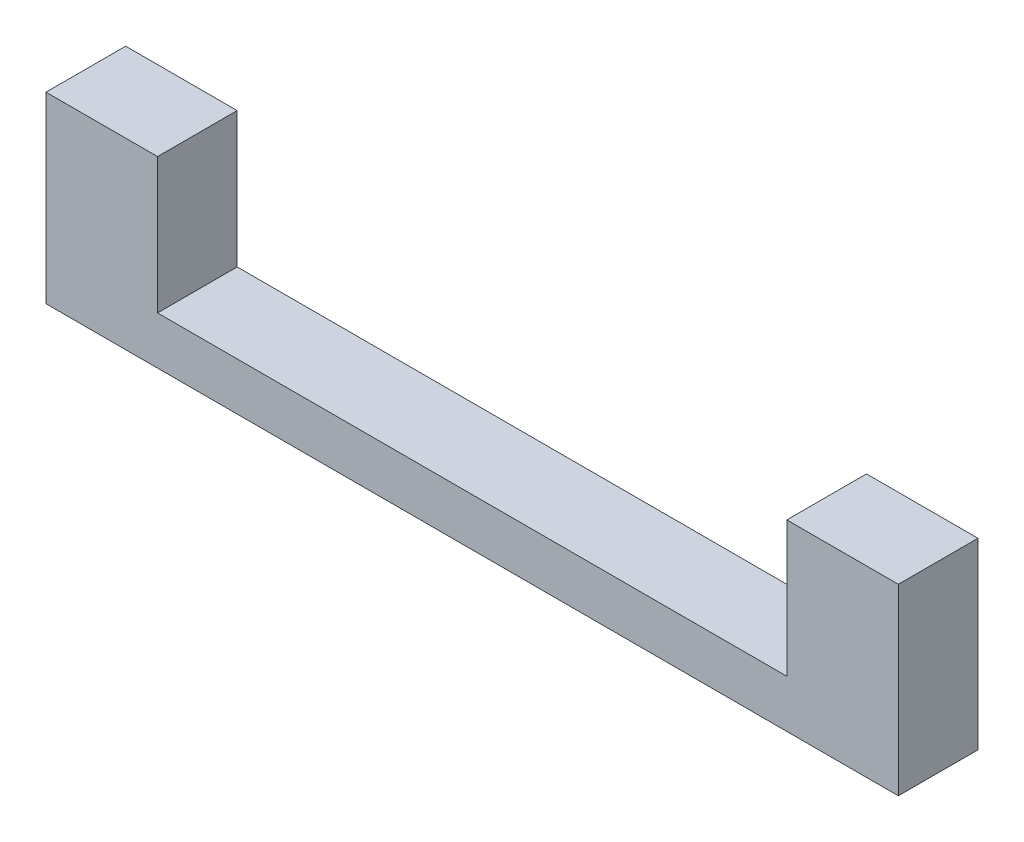
SolidWorks part; units mm, degrees
ref_plane "Front Plane" through (0, 0, 0) normal (0, 0, 1) x (1, 0, 0)
ref_plane "Top Plane" through (0, 0, 0) normal (0, 1, 0) x (1, 0, 0)
ref_plane "Right Plane" through (0, 0, 0) normal (1, 0, 0) x (0, 0, -1)
sketch "Sketch1" plane through (0, 0, 0) normal (1, 0, 0) x (0, 0, -1)
  line L0 (0, 0) -> (1.6017, 0) construction
  line L1 (1.705, 2.9531) -> (-1.705, 2.9531)
  line L2 (-1.705, 2.9531) -> (-3.41, 0)
  line L3 (-3.41, 0) -> (-1.705, -2.9531)
  line L4 (-1.705, -2.9531) -> (1.705, -2.9531)
  line L5 (1.705, -2.9531) -> (3.41, 0)
  line L6 (3.41, 0) -> (1.705, 2.9531)
  line L8 (-4.25, -4.25) -> (4.25, -4.25)
  line L9 (-4.25, -4.25) -> (-4.25, 4.25)
  line L10 (-4.25, 4.25) -> (4.25, 4.25)
  line L11 (4.25, -4.25) -> (4.25, 4.25)
  line L12 (-4.25, -4.25) -> (4.25, 4.25) construction
  line L13 (-4.25, 4.25) -> (4.25, -4.25) construction
  circle A0 centre (0, 0) radius 2.9531 construction
  dimension "D1" = 3.41
  dimension "D2" = 8.5
  dimension "D3" = 8.5
extrude "Boss-Extrude1" add sketch "Sketch1" along normal blind 5
sketch "Sketch2" plane through (0, 0, 0) normal (-1, 0, 0) x (0, 0, 1)
  line L1 (-4.25, -4.25) -> (4.25, -4.25)
  line L2 (-4.25, -4.25) -> (-4.25, 4.25)
  line L3 (-4.25, 4.25) -> (4.25, 4.25)
  line L4 (4.25, -4.25) -> (4.25, 4.25)
  line L5 (-4.25, -4.25) -> (4.25, 4.25) construction
  line L6 (-4.25, 4.25) -> (4.25, -4.25) construction
  point P0 (0, 0)
extrude "Boss-Extrude2" add sketch "Sketch2" along normal blind 2
sketch "Sketch3" plane through (0, 0, 0) normal (1, 0, 0) x (0, 0, -1)
  circle A0 centre (0, 0) radius 1.5
  dimension "D1" = 3
extrude "Cut-Extrude1" cut sketch "Sketch3" against normal blind 2
sketch "Sketch4" plane through (0, -4.25, 0) normal (0, -1, 0) x (1, 0, 0)
  line L0 (5, -4.25) -> (-2, -4.25) construction
  line L1 (-2, 4.25) -> (51.5, 4.25)
  line L2 (-2, 4.25) -> (-2, -4.25)
  line L3 (-2, -4.25) -> (51.5, -4.25)
  line L4 (51.5, 4.25) -> (51.5, -4.25)
  dimension "D1" = 53.5
extrude "Boss-Extrude3" add sketch "Sketch4" along normal blind 3
sketch "Sketch5" plane through (0, -4.25, 0) normal (0, 1, 0) x (1, 0, 0)
  line L0 (51.5, -4.25) -> (5, -4.25) construction
  line L1 (51.5, 4.25) -> (44.5, 4.25)
  line L2 (51.5, 4.25) -> (51.5, -4.25)
  line L3 (51.5, -4.25) -> (44.5, -4.25)
  line L4 (44.5, 4.25) -> (44.5, -4.25)
  dimension "D1" = 7
extrude "Boss-Extrude4" add sketch "Sketch5" along normal up to surface (8.5 mm away) up to face at (1.5, 4.25, 0)
sketch "Sketch6" plane through (44.5, 0, 0) normal (-1, 0, 0) x (0, 0, 1)
  line L0 (-4.25, -4.25) -> (4.25, -4.25) construction
  line L1 (3.41, 0) -> (1.705, 2.9531)
  line L2 (1.705, 2.9531) -> (-1.705, 2.9531)
  line L3 (-1.705, 2.9531) -> (-3.41, 0)
  line L4 (-3.41, 0) -> (-1.705, -2.9531)
  line L5 (-1.705, -2.9531) -> (1.705, -2.9531)
  line L6 (1.705, -2.9531) -> (3.41, 0)
  circle A0 centre (0, 0) radius 2.9531 construction
  dimension "D1" = 3.41
sketch "Sketch8" plane through (0, 0, 0) normal (1, 0, 0) x (0, 0, -1)
  line L0 (-1.705, 2.9531) -> (-3.41, 0) construction
  line L1 (-3.41, 0) -> (-1.705, -2.9531) construction
  line L2 (-1.705, -2.9531) -> (1.705, -2.9531) construction
  line L3 (1.705, -2.9531) -> (3.41, 0) construction
  line L4 (3.41, 0) -> (1.705, 2.9531) construction
  line L5 (1.705, 2.9531) -> (-1.705, 2.9531) construction
  line L6 (-1.705, 2.9531) -> (-3.41, 0)
  line L7 (-3.41, 0) -> (-1.705, -2.9531)
  line L8 (-1.705, -2.9531) -> (1.705, -2.9531)
  line L9 (1.705, -2.9531) -> (3.41, 0)
  line L10 (3.41, 0) -> (1.705, 2.9531)
  line L11 (1.705, 2.9531) -> (-1.705, 2.9531)
  circle A0 centre (0, 0) radius 1.5 construction
  circle A1 centre (0, 0) radius 1.5
extrude "Boss-Extrude5" add sketch "Sketch8" along normal blind 2.5
sketch "Sketch10" plane through (5, 0, 0) normal (1, 0, 0) x (0, 0, -1)
  line L0 (3.41, 0) -> (1.705, 2.9531) construction
  line L1 (1.705, -2.9531) -> (3.41, 0) construction
  line L2 (-1.705, -2.9531) -> (1.705, -2.9531) construction
  line L3 (-3.41, 0) -> (-1.705, -2.9531) construction
  line L4 (-1.705, 2.9531) -> (-3.41, 0) construction
  line L5 (1.705, 2.9531) -> (-1.705, 2.9531) construction
  line L6 (3.41, 0) -> (1.705, 2.9531)
  line L7 (1.705, -2.9531) -> (3.41, 0)
  line L8 (-1.705, -2.9531) -> (1.705, -2.9531)
  line L9 (-3.41, 0) -> (-1.705, -2.9531)
  line L10 (-1.705, 2.9531) -> (-3.41, 0)
  line L11 (1.705, 2.9531) -> (-1.705, 2.9531)
  line L13 (-4.25, 4.25) -> (4.25, 4.25)
  line L14 (-4.25, 4.25) -> (-4.25, -4.25)
  line L15 (-4.25, -4.25) -> (4.25, -4.25)
  line L16 (4.25, 4.25) -> (4.25, -4.25)
extrude "Boss-Extrude7" add sketch "Sketch10" along normal blind 1
sketch "Sketch12" plane through (2.5, 0, 0) normal (1, 0, 0) x (0, 0, -1)
  line L0 (1.705, -2.9531) -> (3.41, 0) construction
  line L1 (3.41, 0) -> (1.705, 2.9531) construction
  line L2 (-1.705, -2.9531) -> (1.705, -2.9531) construction
  line L3 (1.705, 2.9531) -> (-1.705, 2.9531) construction
  line L4 (-3.41, 0) -> (-1.705, -2.9531) construction
  line L5 (-1.705, 2.9531) -> (-3.41, 0) construction
  line L6 (1.705, -2.9531) -> (3.41, 0)
  line L7 (3.41, 0) -> (1.705, 2.9531)
  line L8 (-1.705, -2.9531) -> (1.705, -2.9531)
  line L9 (1.705, 2.9531) -> (-1.705, 2.9531)
  line L10 (-3.41, 0) -> (-1.705, -2.9531)
  line L11 (-1.705, 2.9531) -> (-3.41, 0)
extrude "Cut-Extrude4" cut sketch "Sketch12" against normal blind 0.5
sketch "Sketch14" plane through (6, 0, 0) normal (1, 0, 0) x (0, 0, -1)
  line L1 (-4.25, 4.25) -> (4.25, 4.25)
  line L2 (-4.25, 4.25) -> (-4.25, -4.25)
  line L3 (-4.25, -4.25) -> (4.25, -4.25)
  line L4 (4.25, 4.25) -> (4.25, -4.25)
extrude "Boss-Extrude8" add sketch "Sketch14" against normal up to surface (8 mm away) up to face at (-2, 0, -1.5)
sketch "Sketch15" plane through (6, 0, 0) normal (1, 0, 0) x (0, 0, -1)
  line L1 (-4.25, 4.25) -> (4.25, 4.25)
  line L2 (-4.25, 4.25) -> (-4.25, -4.25)
  line L3 (-4.25, -4.25) -> (4.25, -4.25)
  line L4 (4.25, 4.25) -> (4.25, -4.25)
extrude "Cut-Extrude6" cut sketch "Sketch15" against normal blind 1
sketch "Sketch16" plane through (0, 4.25, 0) normal (0, 1, 0) x (1, 0, 0)
  line L0 (51.5, 4.25) -> (51.5, -4.25) construction
  line L1 (-2, 4.25) -> (51.5, 4.25)
  line L2 (-2, 4.25) -> (-2, 0.75)
  line L3 (-2, 0.75) -> (51.5, 0.75)
  line L4 (51.5, 4.25) -> (51.5, 0.75)
  dimension "D1" = 3.5
extrude "Cut-Extrude7" cut sketch "Sketch16" against normal blind 15
sketch "Sketch17" plane through (44.5, 0, 0) normal (-1, 0, 0) x (0, 0, 1)
  line L1 (-0.75, 4.25) -> (4.25, 4.25)
  line L2 (-0.75, 4.25) -> (-0.75, -4.25)
  line L3 (-0.75, -4.25) -> (4.25, -4.25)
  line L4 (4.25, 4.25) -> (4.25, -4.25)
extrude "Boss-Extrude9" add sketch "Sketch17" against normal up to surface (7 mm away) up to face at (51.5, -1.5, 1.75)
